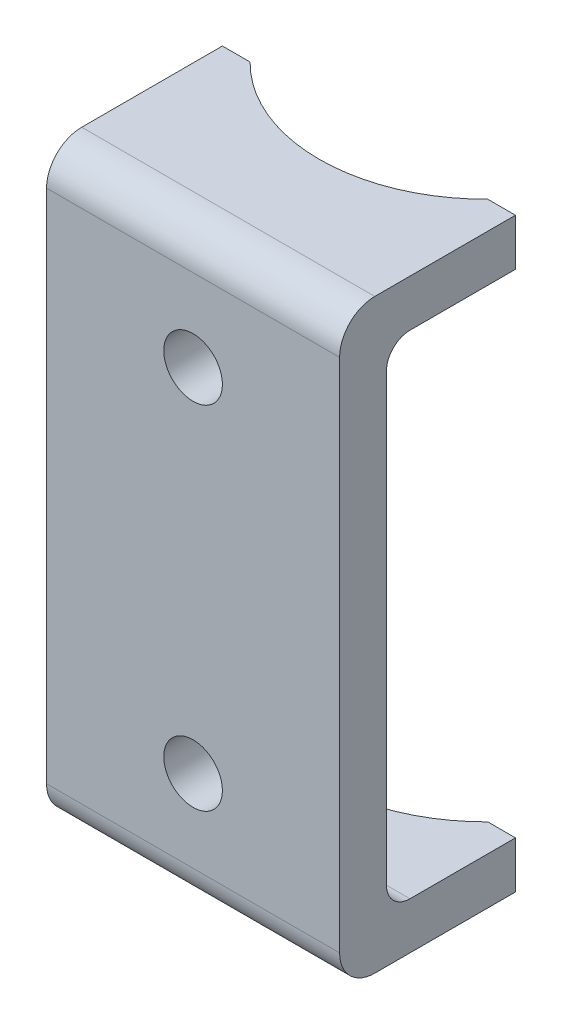
SolidWorks part; units mm, degrees
ref_plane "Front Plane" through (0, 0, 0) normal (0, 0, 1) x (1, 0, 0)
ref_plane "Top Plane" through (0, 0, 0) normal (0, 1, 0) x (1, 0, 0)
ref_plane "Right Plane" through (0, 0, 0) normal (1, 0, 0) x (0, 0, -1)
sketch "Sketch1" plane through (0, 0, 0) normal (1, 0, 0) x (0, 0, -1)
  line L0 (0, 22) -> (0, -22)
  line L1 (15, 25) -> (3, 25)
  line L2 (15, 25) -> (15, 21)
  line L3 (6, 21) -> (15, 21)
  line L4 (4, 19) -> (4, -19)
  line L5 (6, -21) -> (15, -21)
  line L6 (15, -21) -> (15, -25)
  line L7 (15, -25) -> (3, -25)
  arc A0 (0, -22) -> (3, -25) centre (3, -22) ccw
  arc A1 (0, 22) -> (3, 25) centre (3, 22) cw
  arc A2 (4, -19) -> (6, -21) centre (6, -19) ccw
  arc A3 (4, 19) -> (6, 21) centre (6, 19) cw
  point P0 (0, 0)
  point P7 (0, -25)
  point P12 (0, 25)
  dimension "D6" = 3
  dimension "D7" = 2
  dimension "D1" = 50
  dimension "D2" = 4
  dimension "D3" = 4
  dimension "D4" = 4
  dimension "D5" = 15
sketch "Sketch2" plane through (0, 0, 0) normal (0, 0, 1) x (1, 0, 0)
  line L0 (0, 15) -> (0, -15) construction
  circle A0 centre (0, 15) radius 2.5
  circle A3 centre (0, -15) radius 2.5
  point P0 (0, 15.6704)
  dimension "D2" = 5
  dimension "D1" = 30
extrude "Boss-Extrude3" add sketch "Sketch1" along normal mid plane 25
extrude "Cut-Extrude3" cut sketch "Sketch2" against normal up to surface (4 mm away) up to face at (0, 0, -4)
sketch "Sketch3" plane through (0, 0, 0) normal (0, 1, 0) x (1, 0, 0)
  circle A0 centre (0, 25) radius 14.2386
  point P2 (0, 16.962)
  point P3 (0, 19.5193)
  point P4 (0, 19.3333)
  point P6 (0, 21.9371)
  dimension "D1" = 25
extrude "Cut-Extrude4" cut sketch "Sketch3" against normal through all both and the other way through all
